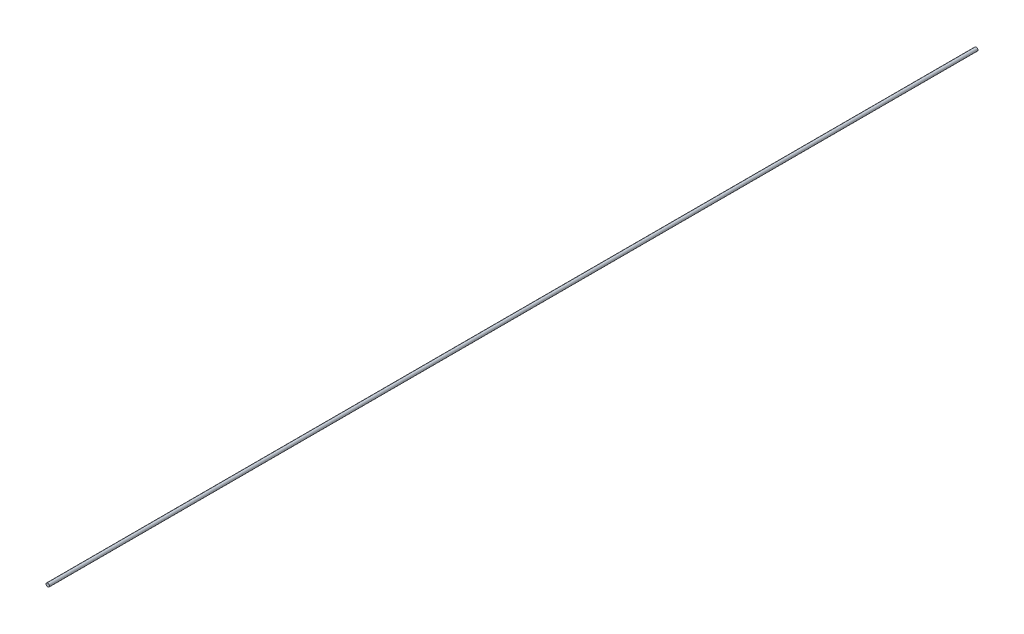
SolidWorks part; units mm, degrees
material "Nylon 101"
ref_plane "Front Plane" through (0, 0, 0) normal (0, 0, 1) x (1, 0, 0)
ref_plane "Top Plane" through (0, 0, 0) normal (0, 1, 0) x (1, 0, 0)
ref_plane "Right Plane" through (0, 0, 0) normal (1, 0, 0) x (0, 0, -1)
sketch "Sketch1" plane through (0, 0, 0) normal (0, 0, 1) x (1, 0, 0)
  circle A0 centre (0, 0) radius 0.5
  dimension "D1" = 1
extrude "Boss-Extrude1" add sketch "Sketch1" along normal blind 270
